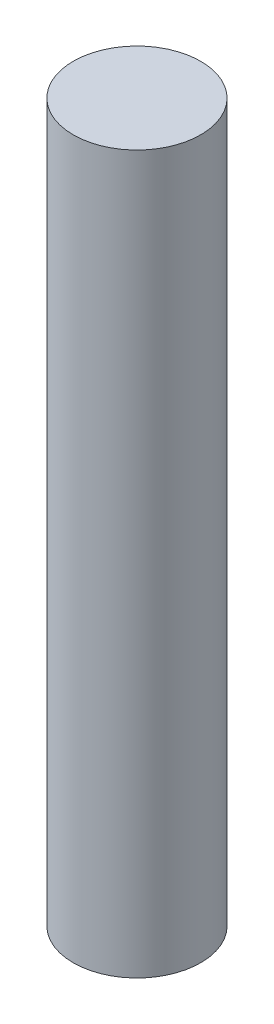
SolidWorks part; units mm, degrees
ref_plane "前视基准面" through (0, 0, 0) normal (0, 0, 1) x (1, 0, 0)
ref_plane "上视基准面" through (0, 0, 0) normal (0, 1, 0) x (1, 0, 0)
ref_plane "右视基准面" through (0, 0, 0) normal (1, 0, 0) x (0, 0, -1)
ref_plane "基准面4" through (0, 0, 0) normal (0, 0, -1) x (-1, 0, 0)
sketch "草图1" plane through (0, 0, 0) normal (0, 0, -1) x (-1, 0, 0)
  line L0 (-64, -45) -> (-60, -45)
  line L1 (-60, -45) -> (-60, 0)
  line L2 (-60, 0) -> (-64, 0)
  line L3 (-64, 0) -> (-64, -45)
  line L4 (-60, -45) -> (-60, 0) construction
revolve "旋转1" add sketch "草图1" angle 360 about L4
